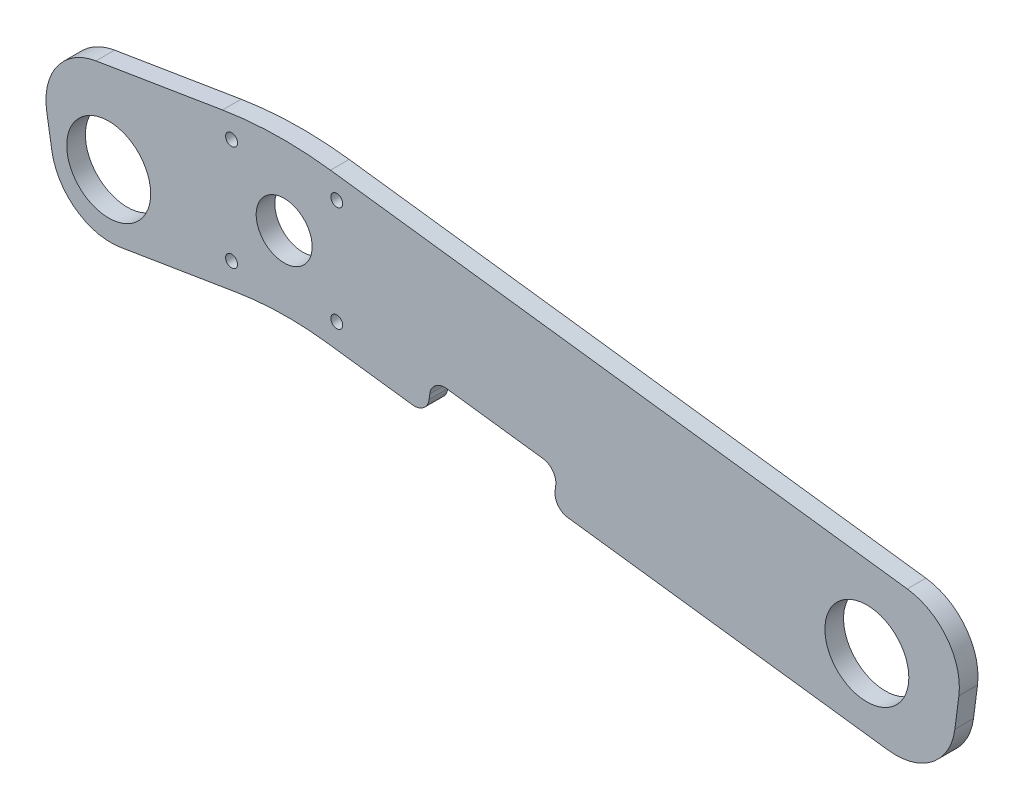
SolidWorks part; units mm, degrees
ref_plane "Front Plane" through (0, 0, 0) normal (0, 0, 1) x (1, 0, 0)
ref_plane "Top Plane" through (0, 0, 0) normal (0, 1, 0) x (1, 0, 0)
ref_plane "Right Plane" through (0, 0, 0) normal (1, 0, 0) x (0, 0, -1)
sketch "Sketch6" plane through (0, 0, 0) normal (0, 0, 1) x (1, 0, 0)
  line L0 (-430.5958, -65.464) -> (-349.1343, -52.1029)
  line L5 (-349.1343, -52.1029) -> (-114.1843, -82.3518)
  line L6 (-430.5958, -65.464) -> (-422.2637, -116.264)
  line L7 (-422.2637, -116.264) -> (-347.3425, -103.9757)
  line L8 (-347.3425, -103.9757) -> (-120.7245, -133.1518)
  line L9 (-120.7245, -133.1518) -> (-114.1843, -82.3518)
  dimension "D1" = 82.55
  dimension "D2" = 234.95
  dimension "D3" = 50.8
  dimension "D4" = 50.8
extrude "Boss-Extrude4" add sketch "Sketch6" along normal blind 6.35
sketch "Sketch8" plane through (0, 0, 6.35) normal (0, 0, 1) x (1, 0, 0)
  line L1 (-254.8984, -115.8775) -> (-253.3674, -103.9852)
  line L2 (-347.3425, -103.9757) -> (-120.7245, -133.1518) construction
  line L3 (-253.3674, -103.9852) -> (-296.2401, -98.4655)
  line L4 (-296.2401, -98.4655) -> (-297.7712, -110.3578)
  line L5 (-297.7712, -110.3578) -> (-254.8984, -115.8775)
  circle A0 centre (-406.2196, -92.0551) radius 14.2875
  circle A1 centre (-148.1006, -105.6486) radius 14.2875
  circle A2 centre (-364.3835, -62.2871) radius 2.032
  circle A3 centre (-364.3843, -98.1011) radius 2.032
  circle A4 centre (-328.5703, -98.1006) radius 2.032
  circle A5 centre (-328.5695, -62.2866) radius 2.032
  circle A6 centre (-346.4769, -80.1939) radius 9.525
  dimension "D1" = 28.575
  dimension "D2" = 28.575
  dimension "D4" = 4.064
  dimension "D6" = 4.064
  dimension "D8" = 4.064
  dimension "D10" = 4.064
  dimension "D12" = 19.05
  dimension "D3" = 258.119
  dimension "D5" = 35.814
  dimension "D7" = 35.814
  dimension "D9" = 35.814
  dimension "D11" = 35.814
extrude "Cut-Extrude7" cut sketch "Sketch8" against normal blind 6.35
fillet "Fillet1" radius 127 1 edges at (-349.1343, -52.1029, 3.175)
fillet "Fillet2" radius 20.32 1 edges at (-430.5958, -65.464, 3.175)
fillet "Fillet3" radius 20.32 1 edges at (-422.2637, -116.264, 3.175)
fillet "Fillet4" radius 20.32 1 edges at (-114.1843, -82.3518, 3.175)
fillet "Fillet5" radius 20.32 1 edges at (-120.7245, -133.1518, 3.175)
fillet "Fillet6" radius 106.68 1 edges at (-347.3425, -103.9757, 3.175)
fillet "Fillet15" radius 5.08 1 edges at (-254.8984, -115.8775, 3.175)
fillet "Fillet16" radius 5.08 1 edges at (-297.7712, -110.3578, 3.175)
fillet "Fillet17" radius 5.08 1 edges at (-296.2401, -98.4655, 3.175)
fillet "Fillet18" radius 5.08 1 edges at (-253.3674, -103.9852, 3.175)
